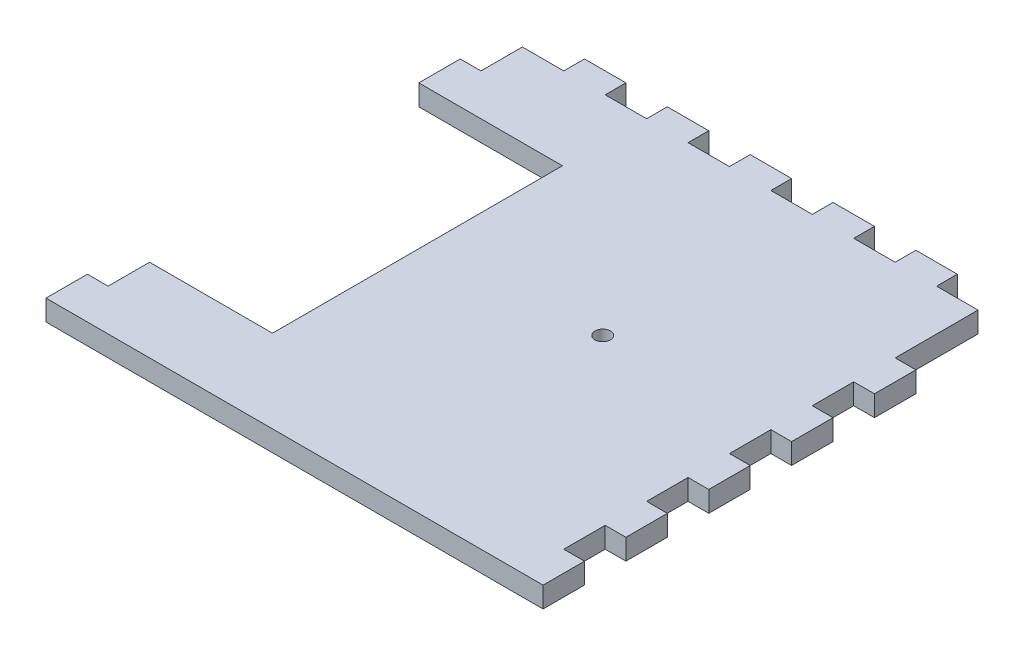
SolidWorks part; units mm, degrees
ref_plane "Front Plane" through (0, 0, 0) normal (0, 0, 1) x (1, 0, 0)
ref_plane "Top Plane" through (0, 0, 0) normal (0, 1, 0) x (1, 0, 0)
ref_plane "Right Plane" through (0, 0, 0) normal (1, 0, 0) x (0, 0, -1)
sketch "Sketch1" plane through (0, 0, 0) normal (0, 1, 0) x (1, 0, 0)
  line L1 (-139.7, -139.7) -> (139.7, -139.7)
  line L2 (-139.7, -139.7) -> (-139.7, 139.7)
  line L3 (-139.7, 139.7) -> (139.7, 139.7)
  line L4 (139.7, -139.7) -> (139.7, 139.7)
  line L5 (-139.7, -139.7) -> (139.7, 139.7) construction
  line L6 (-139.7, 139.7) -> (139.7, -139.7) construction
  point P0 (0, 0)
  dimension "D1" = 279.4
  dimension "D2" = 279.4
extrude "Boss-Extrude1" add sketch "Sketch1" along normal blind 12.7
sketch "Sketch2" plane through (139.7, 0, 0) normal (1, 0, 0) x (0, 0, -1)
  line L0 (-139.7, 12.7) -> (139.7, 12.7) construction
  line L1 (-139.7, 0) -> (-114.3, 0)
  line L2 (-139.7, 0) -> (-139.7, 12.7)
  line L3 (-139.7, 12.7) -> (-114.3, 12.7)
  line L4 (-114.3, 0) -> (-114.3, 12.7)
  dimension "D1" = 25.4
extrude "Boss-Extrude2" add sketch "Sketch2" along normal blind 12.7
pattern_linear "LPattern1" count 5 spacing 50.8 along (0, 0, -1) of "Boss-Extrude2"
mirror "Mirror1" about plane through (0, 0, 0) normal (1, 0, 0) of "LPattern1", "Boss-Extrude2"
sketch "Sketch3" plane through (0, 0, -139.7) normal (0, 0, -1) x (-1, 0, 0)
  line L0 (-139.7, 12.7) -> (139.7, 12.7) construction
  line L1 (-114.3, 12.7) -> (-88.9, 12.7)
  line L2 (-114.3, 12.7) -> (-114.3, 0)
  line L3 (-114.3, 0) -> (-88.9, 0)
  line L4 (-88.9, 12.7) -> (-88.9, 0)
  line L5 (-139.7, 0) -> (139.7, 0) construction
  line L7 (-152.4, 0) -> (-152.4, 12.7) construction
  dimension "D1" = 38.1
  dimension "D2" = 25.4
extrude "Boss-Extrude3" add sketch "Sketch3" along normal blind 12.7
pattern_linear "LPattern2" count 5 spacing 50.8 along (-1, 0, 0) of "Boss-Extrude3"
sketch "Sketch6" plane through (0, 12.7, 0) normal (0, 1, 0) x (1, 0, 0)
  line L0 (38.1, 139.7) -> (12.7, 139.7) construction
  line L1 (139.7, -12.7) -> (139.7, 12.7) construction
  circle A0 centre (38.1, 11.176) radius 4.7625
  dimension "D1" = 128.524
  dimension "D3" = 9.525
  dimension "D2" = 101.6
extrude "Cut-Extrude1" cut sketch "Sketch6" against normal through all
sketch "Sketch8" plane through (0, 12.7, 0) normal (0, 1, 0) x (1, 0, 0)
  line L1 (-152.4, 88.9) -> (-64.3339, 88.9)
  line L2 (-152.4, 88.9) -> (-152.4, -88.9)
  line L3 (-152.4, -88.9) -> (-64.3339, -88.9)
  line L4 (-64.3339, 88.9) -> (-64.3339, -88.9)
  dimension "D1" = 177.8
extrude "Cut-Extrude3" cut sketch "Sketch8" against normal through all
sketch "Sketch7" plane through (0, 12.7, 0) normal (0, 1, 0) x (1, 0, 0)
  line L2 (-114.3, 139.7) -> (-139.7, 139.7) construction
  line L3 (-139.7, 139.7) -> (-139.7, 88.9) construction
  circle A0 centre (-101.6, 65.278) radius 5.08
  circle A1 centre (-101.6, 27.686) radius 5.08
  dimension "D1" = 10.16
  dimension "D2" = 10.16
  dimension "D3" = 38.1
  dimension "D5" = 37.592
  dimension "D6" = 74.422
sketch "Sketch9" plane through (-139.7, 0, 0) normal (-1, 0, 0) x (0, 0, 1)
  line L0 (153.67, 0) -> (-153.67, 0) construction
  line L1 (-88.9, 12.7) -> (-114.3, 12.7)
  line L2 (-88.9, 12.7) -> (-88.9, 0)
  line L3 (-88.9, 0) -> (-114.3, 0)
  line L4 (-114.3, 12.7) -> (-114.3, 0)
  dimension "D1" = 25.4
extrude "Boss-Extrude4" add sketch "Sketch9" along normal blind 12.7
